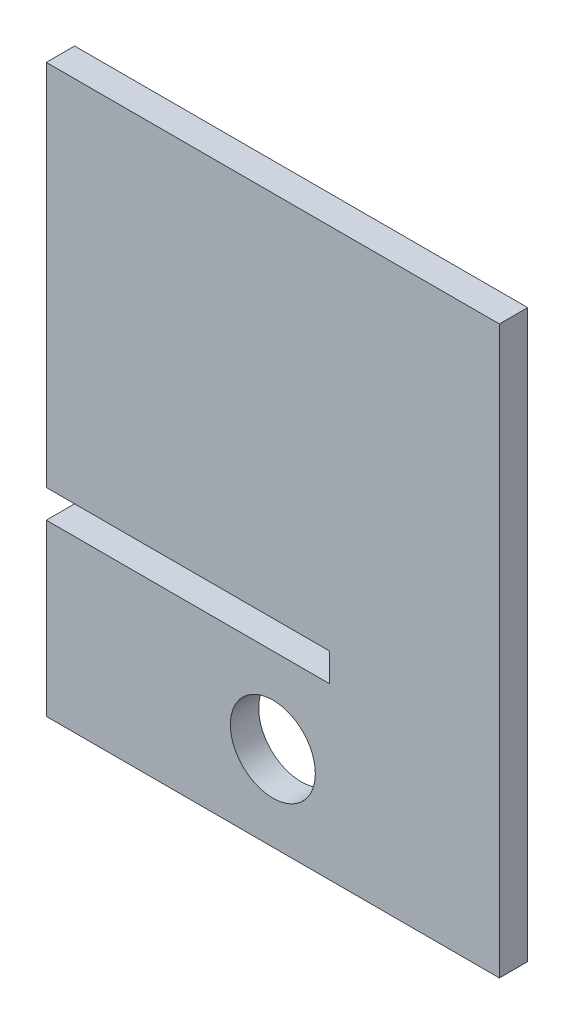
SolidWorks part; units mm, degrees
ref_plane "Plan de face" through (0, 0, 0) normal (0, 0, 1) x (1, 0, 0)
ref_plane "Plan de dessus" through (0, 0, 0) normal (0, 1, 0) x (1, 0, 0)
ref_plane "Plan de droite" through (0, 0, 0) normal (1, 0, 0) x (0, 0, -1)
sketch "Esquisse1" plane through (0, 0, 0) normal (0, 0, 1) x (1, 0, 0)
  line L0 (-41.5573, -39.1162) -> (-41.5573, -69.1162)
  line L1 (-41.5573, 30.8838) -> (38.4427, 30.8838)
  line L2 (-41.5573, -34.1162) -> (-41.5573, 30.8838)
  line L3 (-41.5573, -69.1162) -> (38.4427, -69.1162)
  line L4 (38.4427, 30.8838) -> (38.4427, -69.1162)
  line L5 (-41.5573, -34.1162) -> (8.4427, -34.1162)
  line L7 (-41.5573, -39.1162) -> (8.4427, -39.1162)
  line L8 (8.4427, -34.1162) -> (8.4427, -39.1162)
  circle A0 centre (-1.5573, -54.1162) radius 7.5
  dimension "D5" = 15
  dimension "D1" = 80
  dimension "D2" = 100
  dimension "D3" = 50
  dimension "D4" = 5
  dimension "D6" = 40
  dimension "D7" = 15
  dimension "D8" = 30
extrude "Boss.-Extru.1" add sketch "Esquisse1" along normal blind 5
